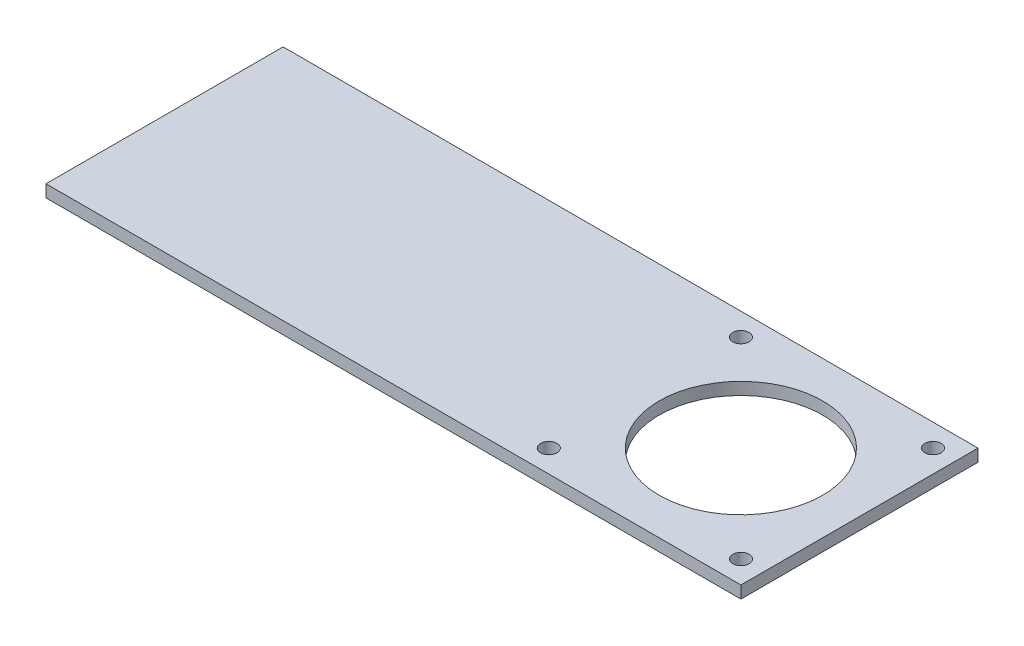
SolidWorks part; units mm, degrees
material "1060 Alloy"
ref_plane "Front Plane" through (0, 0, 0) normal (0, 0, 1) x (1, 0, 0)
ref_plane "Top Plane" through (0, 0, 0) normal (0, 1, 0) x (1, 0, 0)
ref_plane "Right Plane" through (0, 0, 0) normal (1, 0, 0) x (0, 0, -1)
sketch "Sketch1" plane through (0, 0, 0) normal (0, 0, 1) x (1, 0, 0)
  line L1 (-91.0636, 0) -> (78.9364, 0)
  line L2 (-91.0636, 0) -> (-91.0636, -3)
  line L3 (-91.0636, -3) -> (78.9364, -3)
  line L4 (78.9364, 0) -> (78.9364, -3)
  dimension "D1" = 3
  dimension "D2" = 170
extrude "Boss-Extrude1" add sketch "Sketch1" along normal blind 58
sketch "Sketch2" plane through (0, 0, 0) normal (0, 1, 0) x (1, 0, 0)
  line L0 (78.9364, 0) -> (73.4364, 0) construction
  line L1 (78.9364, 0) -> (-91.0636, 0) construction
  line L2 (73.4364, 0) -> (73.4364, -5.5) construction
  line L3 (78.9364, -29) -> (9.5823, -29) construction
  line L4 (78.9364, -58) -> (78.9364, 0) construction
  line L5 (78.9364, -58) -> (49.9364, -58) construction
  line L6 (78.9364, -58) -> (-91.0636, -58) construction
  line L7 (49.9364, -58) -> (49.9364, 0) construction
  circle A0 centre (73.4364, -5.5) radius 2
  circle A1 centre (73.4364, -52.5) radius 2
  circle A2 centre (26.4364, -52.5) radius 2
  circle A3 centre (26.4364, -5.5) radius 2
  circle A4 centre (49.9364, -29) radius 20
  dimension "D4" = 4
  dimension "D5" = 40
  dimension "D1" = 5.5
  dimension "D2" = 5.5
  dimension "D3" = 29
extrude "Cut-Extrude1" cut sketch "Sketch2" against normal blind 58
